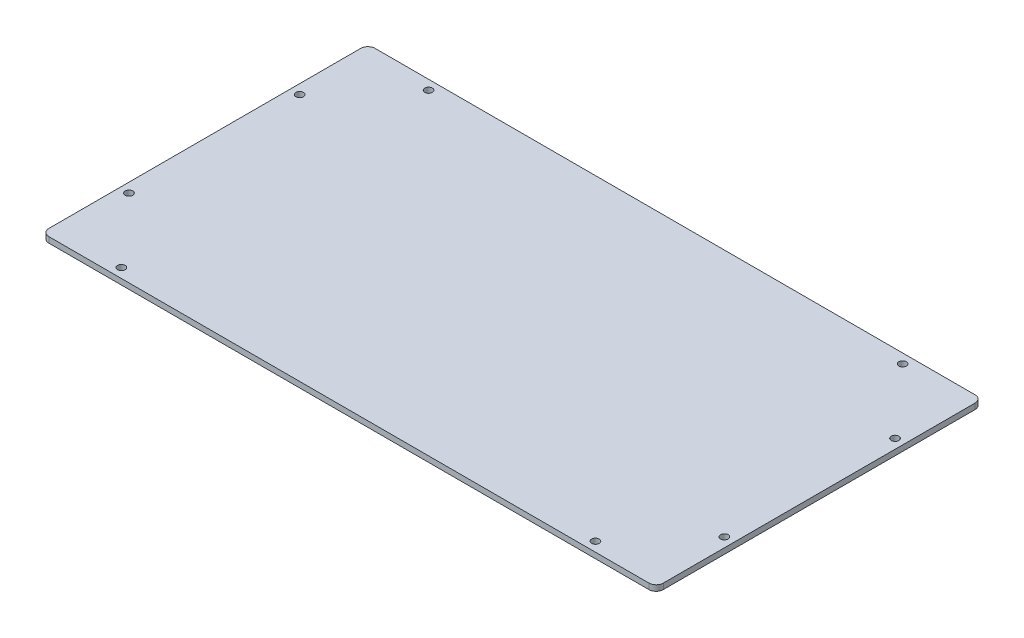
SolidWorks part; units mm, degrees
ref_plane "前视基准面" through (0, 0, 0) normal (0, 0, 1) x (1, 0, 0)
ref_plane "上视基准面" through (0, 0, 0) normal (0, 1, 0) x (1, 0, 0)
ref_plane "右视基准面" through (0, 0, 0) normal (1, 0, 0) x (0, 0, -1)
ref_plane "基准面1" through (0, -3, 0) normal (0, -1, 0) x (1, 0, 0)
sketch "草图1" plane through (0, -3, 0) normal (0, -1, 0) x (1, 0, 0)
  line L0 (162, -82.2) -> (162, 82.2)
  line L1 (158.2, 86) -> (-158.2, 86)
  line L2 (-162, 82.2) -> (-162, -82.2)
  line L3 (-158.2, -86) -> (158.2, -86)
  circle A0 centre (157, 45) radius 2
  circle A1 centre (157, -45) radius 2
  circle A2 centre (125, -81) radius 2
  circle A3 centre (-125, -81) radius 2
  circle A4 centre (-157, -45) radius 2
  circle A5 centre (-157, 45) radius 2
  circle A6 centre (125, 81) radius 2
  circle A7 centre (-125, 81) radius 2
  arc A8 (162, 82.2) -> (158.2, 86) centre (158.2, 82.2) ccw
  arc A9 (-158.2, 86) -> (-162, 82.2) centre (-158.2, 82.2) ccw
  arc A10 (-162, -82.2) -> (-158.2, -86) centre (-158.2, -82.2) ccw
  arc A11 (158.2, -86) -> (162, -82.2) centre (158.2, -82.2) ccw
extrude "凸台-拉伸1" add sketch "草图1" against normal blind 3
